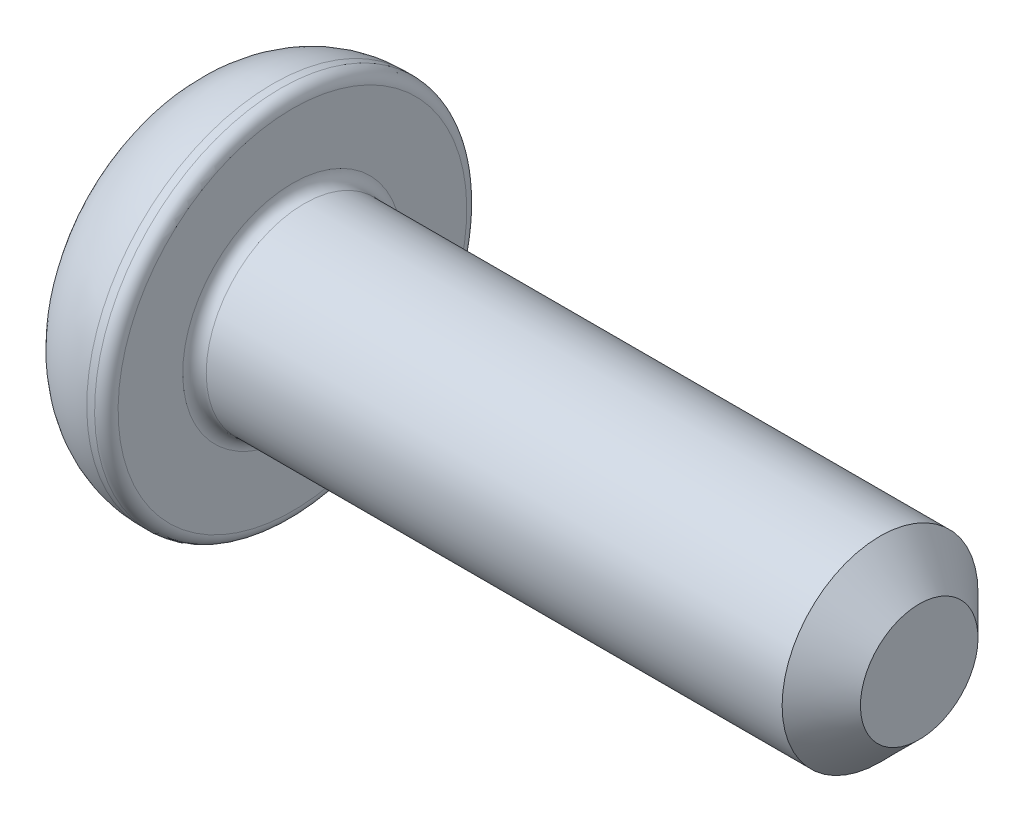
SolidWorks part; units mm, degrees
ref_plane "Спереди" through (0, 0, 0) normal (0, 0, 1) x (1, 0, 0)
ref_plane "Сверху" through (0, 0, 0) normal (0, 1, 0) x (1, 0, 0)
ref_plane "Справа" through (0, 0, 0) normal (1, 0, 0) x (0, 0, -1)
sketch "Эскиз1" plane through (0, 0, 0) normal (0, 0, 1) x (1, 0, 0)
  line L0 (0, 0) -> (0, 3.625)
  line L1 (2.1, 4.75) -> (2.6, 4.75)
  line L2 (2.6, 4.75) -> (2.6, 2.5)
  line L3 (2.6, 2.5) -> (18.6, 2.5)
  line L4 (18.6, 2.5) -> (18.6, 0)
  line L5 (18.6, 0) -> (0, 0) construction
  line L6 (0, 0) -> (18.6, 0)
  arc A0 (0, 3.625) -> (2.1, 4.75) centre (2.1, 2.2275) cw
  point P9 (2.6, 3.625)
  dimension "D1" = 0.5
  dimension "D2" = 5
  dimension "D3" = 9.5
  dimension "D5" = 2.6
  dimension "D6" = 16
revolve "Повернуть1" add sketch "Эскиз1" angle 360 about L5
cosmetic thread "Условное изображение резьбы1" parameters "D2"=4.11
sketch "Эскиз2" plane through (0, 0, 0) normal (-1, 0, 0) x (0, 0, 1)
  line L1 (0.866, 1.5) -> (-0.866, 1.5)
  line L2 (-0.866, 1.5) -> (-1.7321, 0)
  line L3 (-1.7321, 0) -> (-0.866, -1.5)
  line L4 (-0.866, -1.5) -> (0.866, -1.5)
  line L5 (0.866, -1.5) -> (1.7321, 0)
  line L6 (1.7321, 0) -> (0.866, 1.5)
  circle A0 centre (0, 0) radius 1.5 construction
  dimension "D1" = 3
extrude "Вырез-Вытянуть1" cut sketch "Эскиз2" against normal blind 1.5
fillet "Скругление1" radius 0.3 2 edges at (2.6, 2.5, 0) (2.6, 4.75, 0)
chamfer "Фаска1" distance 1 angle 45 1 edges at (18.6, 2.5, 0)
